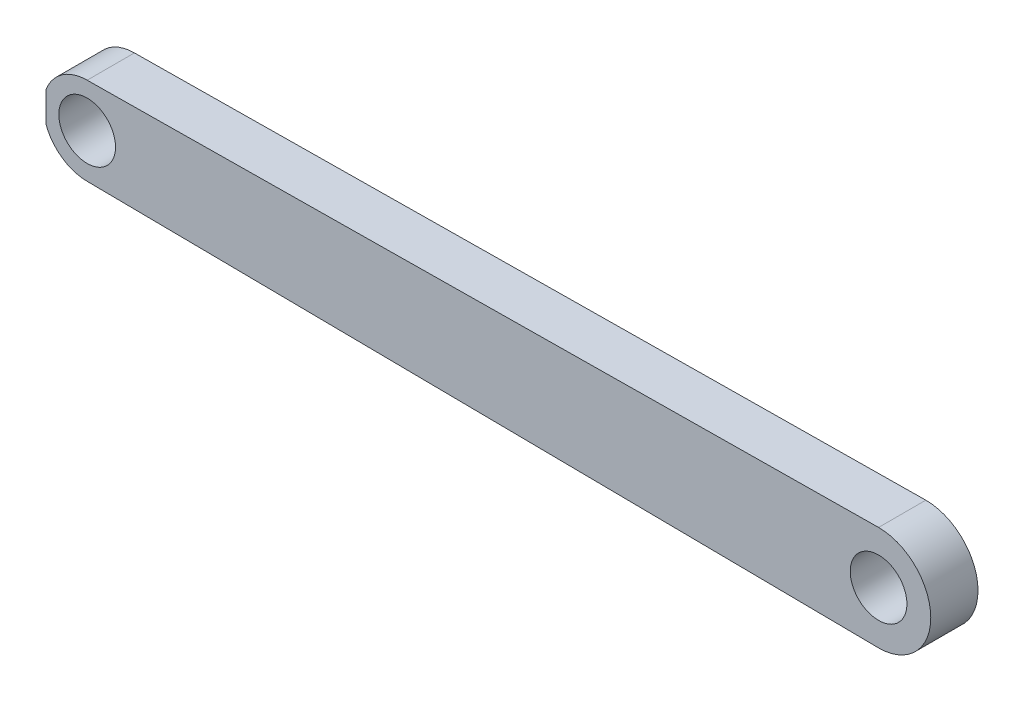
SolidWorks part; units mm, degrees
material "ABS"
ref_plane "Płaszczyzna przednia" through (0, 0, 0) normal (0, 0, 1) x (1, 0, 0)
ref_plane "Płaszczyzna górna" through (0, 0, 0) normal (0, 1, 0) x (1, 0, 0)
ref_plane "Płaszczyzna prawa" through (0, 0, 0) normal (1, 0, 0) x (0, 0, -1)
sketch "Szkic1" plane through (0, 0, 0) normal (0, 0, 1) x (1, 0, 0)
  line L0 (-3, 0) -> (83.7624, 0) construction
  line L1 (40.3812, 0) -> (40.3812, 21.7565) construction
  line L2 (83.7624, -5.5226) -> (0, -4.6352)
  line L3 (83.7624, 5.5226) -> (0, 4.6352)
  circle A0 centre (0, 0) radius 3
  circle A1 centre (83.7624, 0) radius 3
  circle A2 centre (83.7624, 0) radius 5.5226
  circle A3 centre (0, 0) radius 4.6352
  dimension "D1" = 83.7624
  dimension "D2" = 6
  dimension "D3" = 5.5226
  dimension "D4" = 4.6352
extrude "Dodanie-wyciągnięcie1" add sketch "Szkic1" along normal blind 5
sketch "Szkic2" plane through (0, 0, 0) normal (0, 0, 1) x (1, 0, 0)
  line L0 (196.2931, 0) -> (-6.6873, 0) construction
  line L1 (192.8293, 4.1341) -> (192.8293, -3.3715)
  line L2 (-4.3568, -2.5646) -> (-4.3568, 2.4871)
  line L4 (-4.3568, 2.4871) -> (-5.0086, 2.4871)
  line L5 (-4.3568, 2.4871) -> (-4.3568, -2.5646)
  line L6 (-4.3568, -2.5646) -> (-5.0086, -2.5646)
  line L7 (-5.0086, 2.4871) -> (-5.0086, -2.5646)
  line L8 (192.8293, -3.3715) -> (194.4479, -3.3715)
  line L9 (192.8293, -3.3715) -> (192.8293, 4.1341)
  line L10 (192.8293, 4.1341) -> (194.4479, 4.1341)
  line L11 (194.4479, -3.3715) -> (194.4479, 4.1341)
extrude "Wytnij-wyciągnięcie3" cut sketch "Szkic2" along normal through all contours L0 L11 L10 L1 | L11 L0 L9 L8 | L0 L5 L4 L7 | L2 L0 L7 L6
